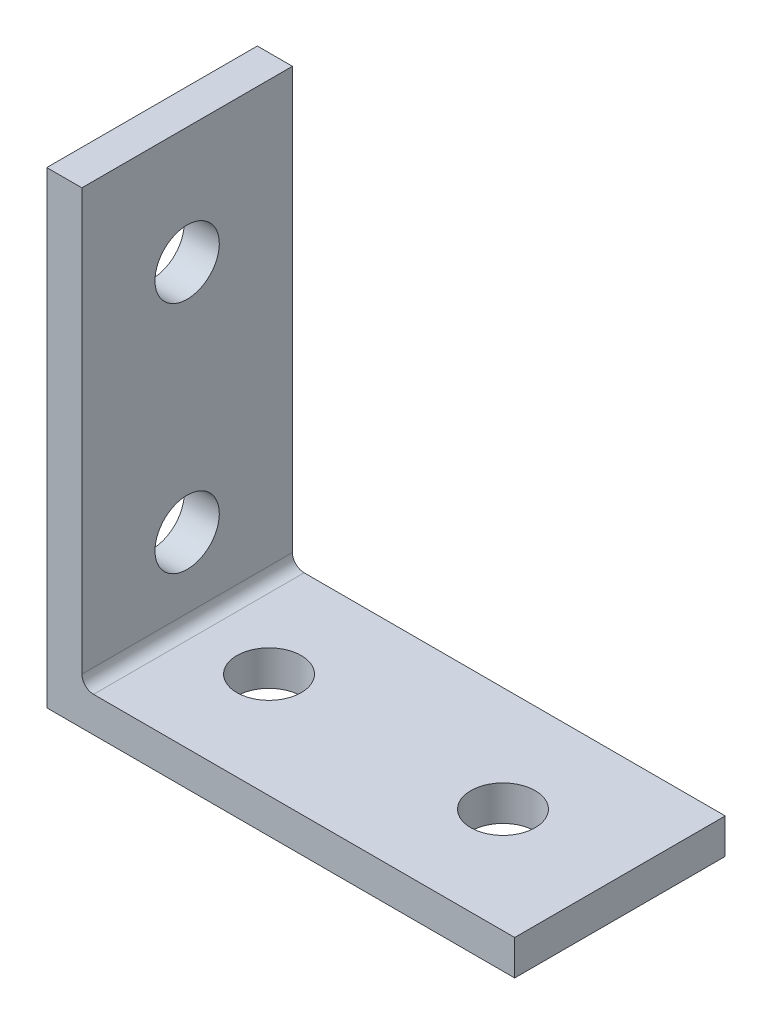
SolidWorks part; units mm, degrees
material "6063-T5"
ref_plane "Front Plane" through (0, 0, 0) normal (0, 0, 1) x (1, 0, 0)
ref_plane "Top Plane" through (0, 0, 0) normal (0, 1, 0) x (1, 0, 0)
ref_plane "Right Plane" through (0, 0, 0) normal (1, 0, 0) x (0, 0, -1)
sketch "Sketch1" plane through (0, 0, 0) normal (0, 0, 1) x (1, 0, 0)
  line L0 (0, 0) -> (0, 40)
  line L1 (0, 40) -> (3, 40)
  line L2 (3, 40) -> (3, 4)
  line L3 (4, 3) -> (40, 3)
  line L4 (40, 3) -> (40, 0)
  line L5 (40, 0) -> (0, 0)
  arc A0 (4, 3) -> (3, 4) centre (4, 4) cw
  dimension "D3" = 1
  dimension "D1" = 3
  dimension "D2" = 40
extrude "Boss-Extrude1" add sketch "Sketch1" along normal mid plane 18
sketch "Sketch2" plane through (3, 0, 0) normal (1, 0, 0) x (0, 0, -1)
  line L0 (-9, 0) -> (9, 0) construction
  line L1 (-9, 4) -> (-9, 40) construction
  circle A0 centre (0, 10) radius 2.75
  circle A1 centre (0, 30) radius 2.75
  dimension "D1" = 10
  dimension "D3" = 5.5
  dimension "D2" = 20
  dimension "D4" = 9
extrude "Cut-Extrude1" cut sketch "Sketch2" against normal through all
sketch "Sketch3" plane through (0, 3, 0) normal (0, 1, 0) x (1, 0, 0)
  line L0 (0, -9) -> (0, 9) construction
  circle A0 centre (10, 0) radius 2.75
  circle A1 centre (30, 0) radius 2.75
  dimension "D1" = 10
  dimension "D3" = 5.5
  dimension "D2" = 20
extrude "Cut-Extrude2" cut sketch "Sketch3" against normal through all
